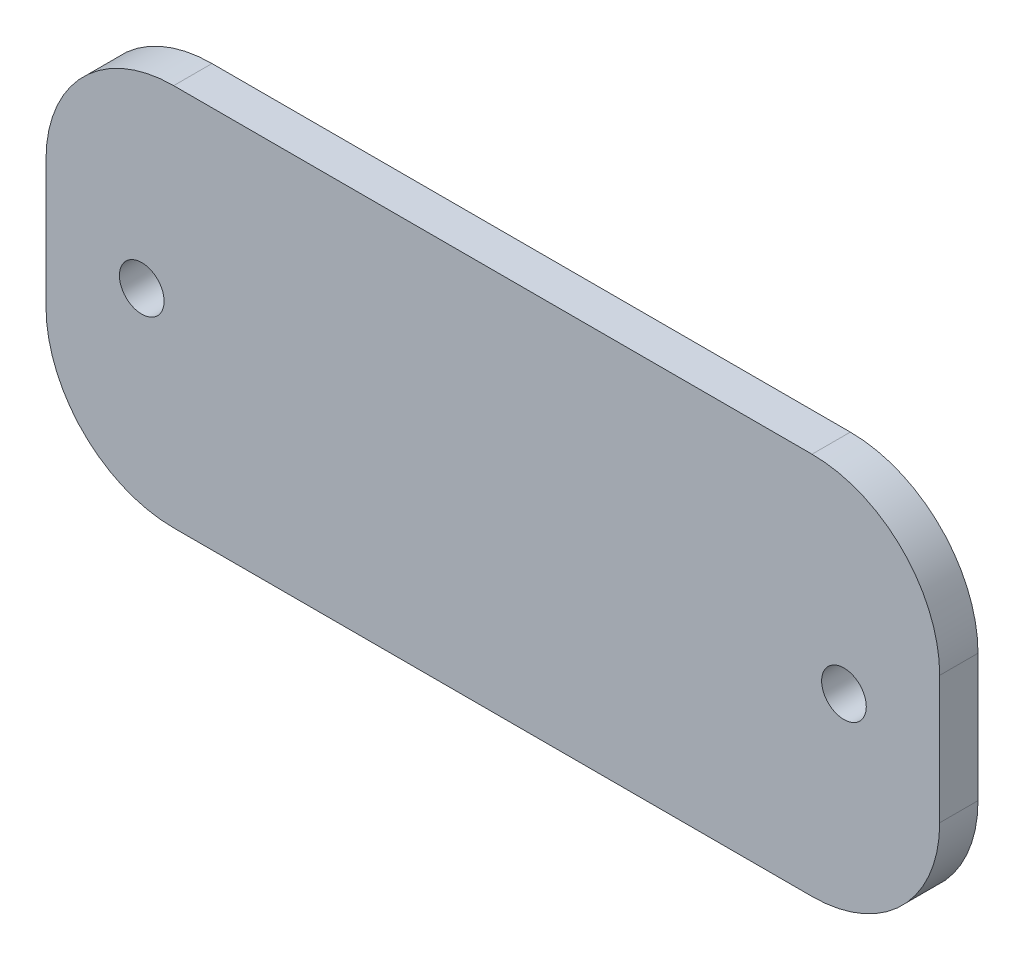
SolidWorks part; units mm, degrees
ref_plane "Front Plane" through (0, 0, 0) normal (0, 0, 1) x (1, 0, 0)
ref_plane "Top Plane" through (0, 0, 0) normal (0, 1, 0) x (1, 0, 0)
ref_plane "Right Plane" through (0, 0, 0) normal (1, 0, 0) x (0, 0, -1)
sketch "Sketch1" plane through (0, 0, 0) normal (0, 0, 1) x (1, 0, 0)
  line L1 (-25, 15) -> (25, 15)
  line L2 (-35, 5) -> (-35, -5)
  line L3 (-25, -15) -> (25, -15)
  line L4 (35, 5) -> (35, -5)
  line L5 (-35, 15) -> (35, -15) construction
  line L6 (-35, -15) -> (35, 15) construction
  arc A0 (25, 15) -> (35, 5) centre (25, 5) cw
  arc A1 (25, -15) -> (35, -5) centre (25, -5) ccw
  arc A2 (-35, -5) -> (-25, -15) centre (-25, -5) ccw
  arc A3 (-25, 15) -> (-35, 5) centre (-25, 5) ccw
  point P0 (0, 0)
  dimension "D3" = 10
  dimension "D1" = 70
  dimension "D2" = 30
extrude "Boss-Extrude1" add sketch "Sketch1" along normal blind 3
sketch "Sketch2" plane through (0, 0, 3) normal (0, 0, 1) x (1, 0, 0)
  line L0 (-27.5, 0) -> (27.5, 0) construction
  circle A0 centre (-27.5, 0) radius 1.75
  circle A1 centre (27.5, 0) radius 1.75
  dimension "D2" = 3.5
  dimension "D1" = 55
extrude "Cut-Extrude1" cut sketch "Sketch2" against normal blind 3
